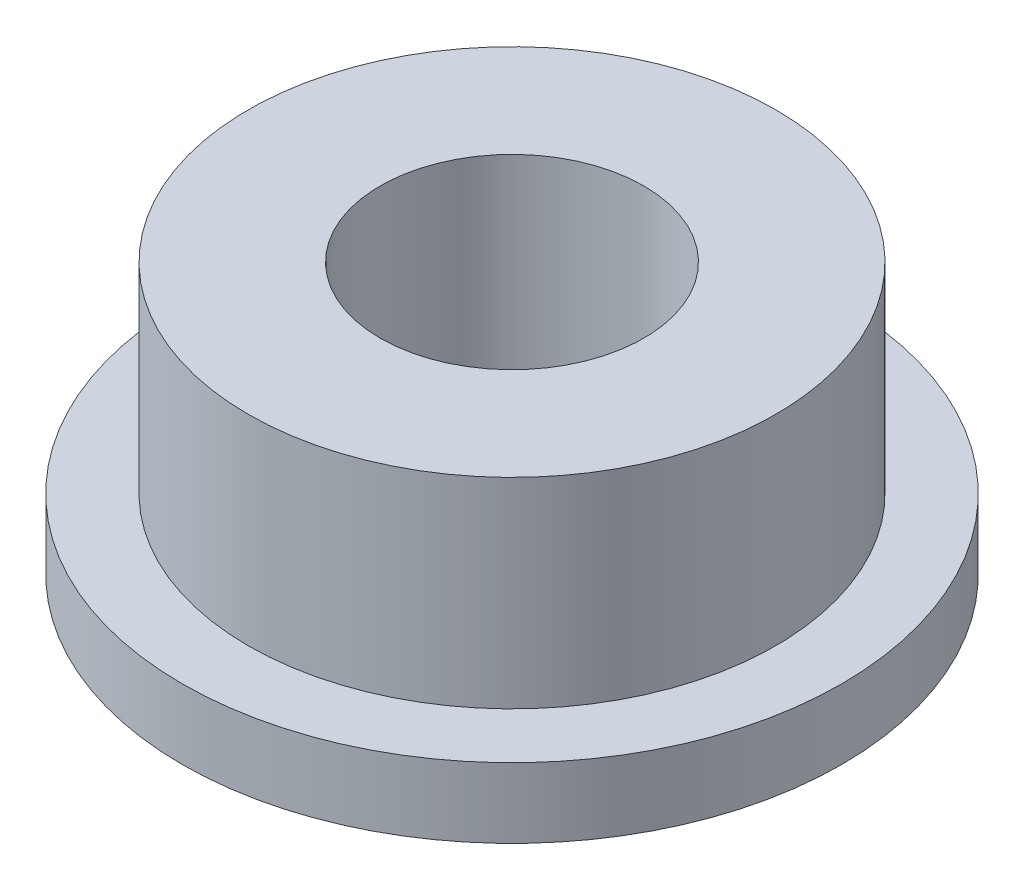
SolidWorks part; units mm, degrees
ref_plane "Front Plane" through (0, 0, 0) normal (0, 0, 1) x (1, 0, 0)
ref_plane "Top Plane" through (0, 0, 0) normal (0, 1, 0) x (1, 0, 0)
ref_plane "Right Plane" through (0, 0, 0) normal (1, 0, 0) x (0, 0, -1)
sketch "Sketch1" plane through (0, 0, 0) normal (0, 0, 1) x (1, 0, 0)
  line L0 (0, 0) -> (0, 6.2518) construction
  line L1 (-5, 0) -> (-2, 0)
  line L2 (-2, 0) -> (-2, 4.1)
  line L3 (-2, 4.1) -> (-4, 4.1)
  line L4 (-4, 4.1) -> (-4, 1.06)
  line L5 (-4, 1.06) -> (-5, 1.06)
  line L6 (-5, 1.06) -> (-5, 0)
  dimension "D1" = 1.06
  dimension "D2" = 5
  dimension "D3" = 4
  dimension "D4" = 2
  dimension "D5" = 4.1
revolve "Revolve1" add sketch "Sketch1" angle 360 about L0
